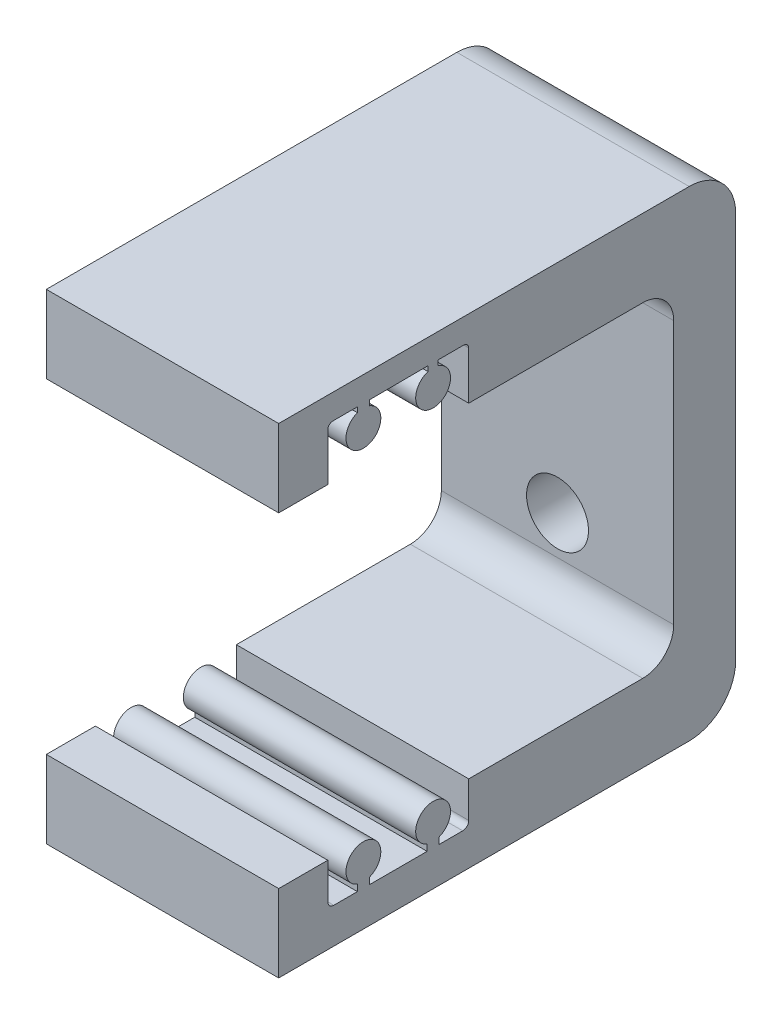
SolidWorks part; units mm, degrees
material "ABS"
ref_plane "Plano frontal" through (0, 0, 0) normal (0, 0, 1) x (1, 0, 0)
ref_plane "Plano superior" through (0, 0, 0) normal (0, 1, 0) x (1, 0, 0)
ref_plane "Plano direito" through (0, 0, 0) normal (1, 0, 0) x (0, 0, -1)
sketch "Esboço1" plane through (0, 0, 0) normal (0, 0, 1) x (1, 0, 0)
  line L0 (-15, 31) -> (-15, -31)
  line L1 (-15, -21) -> (15, -21)
  line L2 (-15, -21) -> (-15, 21)
  line L3 (-15, 21) -> (15, 21)
  line L4 (15, -21) -> (15, 21)
  line L5 (-15, -21) -> (15, 21) construction
  line L6 (-15, 21) -> (15, -21) construction
  line L7 (-15, -31) -> (15, -31)
  line L8 (15, -31) -> (15, 31)
  line L9 (15, 31) -> (-15, 31)
  point P0 (0, 0)
  point P10 (-15, 0)
  dimension "D1" = 42
  dimension "D2" = 30
  dimension "D3" = 10
extrude "Ressalto-extrusão1" add sketch "Esboço1" along normal blind 59 contours L8 L9 L0 L3 | L7 L8 L1 L0
sketch "Esboço2" plane through (0, 0, 0) normal (0, 0, -1) x (-1, 0, 0)
  line L0 (15, -21) -> (-15, -21) construction
  line L1 (15, 31) -> (15, -31) construction
  line L2 (15, 21) -> (-15, 21) construction
  line L3 (-15, -21) -> (-15, 21) construction
  line L4 (15, -21) -> (-15, -21)
  line L5 (15, 31) -> (15, -31)
  line L6 (15, 21) -> (-15, 21)
  line L7 (-15, -21) -> (-15, 21)
  line L8 (-15, 21) -> (-15, 31)
  line L9 (-15, 31) -> (15, 31)
  line L10 (-15, -21) -> (-15, -31)
  line L11 (-15, -31) -> (15, -31)
  line L12 (15, -21) -> (-15, -21)
  line L13 (-15, 21) -> (15, 21)
  line L14 (15, -21) -> (-15, -21)
  line M2 (-15, 21) -> (15, 21)
extrude "Ressalto-extrusão2" add sketch "Esboço2" against normal blind 8 contours L7 L4 L5 M2
sketch "Esboço3" plane through (-15, 0, 0) normal (-1, 0, 0) x (0, 0, 1)
  line L0 (31.2729, 21) -> (33.5, 21)
  line L1 (59, 21) -> (8, 21) construction
  line L2 (34.4643, 21) -> (34.4643, 27.1808)
  line L3 (38.4075, 27.8215) -> (38.4075, 27.1622)
  line L4 (39.7211, 27.8215) -> (39.7211, 27.1622)
  line L6 (0, 0) -> (64.8544, 0) construction
  line L7 (47.295, 27.1246) -> (47.295, 27.7839)
  line L8 (48.8337, 27.1246) -> (48.8337, 27.7839)
  line L9 (52.5643, 26.27) -> (52.5643, 20.7683) construction
  line L10 (52.5643, 21) -> (54.6977, 21)
  line L11 (33.5, 21) -> (52.5643, 21)
  line L13 (35.105, 27.8215) -> (38.1075, 27.8215)
  line L14 (38.1075, 27.8215) -> (40.0211, 27.8215)
  line L15 (40.0211, 27.8215) -> (48.8534, 27.7758)
  line L16 (48.8534, 27.7758) -> (48.8337, 27.7839)
  line L17 (48.8337, 27.7839) -> (52.0143, 27.7839)
  line L18 (52.6643, 27.1338) -> (52.6643, 21)
  line L19 (0, 31) -> (0, -31) construction
  line L20 (44.3337, -27.7122) -> (44.3337, -28.817) construction
  line L21 (52.6643, -25.6493) -> (52.6643, -20.77)
  line L22 (49.2154, -26.4238) -> (51.8898, -26.4238)
  line L23 (48.5337, -26.4238) -> (49.2154, -26.4238)
  line L24 (40.1337, -26.4238) -> (48.5337, -26.4238)
  line L25 (37.995, -26.4238) -> (40.1337, -26.4238)
  line L26 (35.2389, -26.4238) -> (37.995, -26.4238)
  line L27 (34.4643, -20.7704) -> (34.4643, -25.6493)
  line L28 (34.5, -20.77) -> (52.5643, -20.77)
  line L29 (52.5643, -20.77) -> (54.6977, -20.77)
  line L30 (47.295, -25.5846) -> (47.295, -26.4238)
  line L31 (48.8337, -27.7122) -> (48.8337, -25.5846)
  line L32 (39.8337, -26.4238) -> (39.8337, -25.5846)
  line L33 (38.295, -26.4238) -> (38.295, -25.5846)
  line L34 (34.4643, -20.7704) -> (34.5, -20.77)
  line L35 (31.2729, -20.77) -> (34.5, -20.77)
  line L36 (34.5643, 20.7683) -> (34.5643, 26.27) construction
  line L37 (34.5643, -19.2283) -> (34.5643, -24.73) construction
  line L38 (34.4643, -20.7704) -> (34.5, -20.77)
  line L39 (52.6643, -20.77) -> (52.5643, -20.77)
  line L40 (46.995, -25.73) -> (46.995, -26.4238) construction
  line L41 (49.1337, -25.73) -> (49.1337, -26.4238) construction
  line L42 (40.1337, -25.73) -> (40.1337, -26.4238) construction
  line L43 (37.995, -25.73) -> (37.995, -26.4238) construction
  arc A0 (38.4075, 27.1622) -> (39.7211, 27.1622) centre (39.0643, 25.0102) ccw
  arc A1 (47.295, 27.1246) -> (48.8337, 27.1246) centre (48.0643, 25.0102) ccw
  arc A2 (51.8898, -26.4238) -> (52.6643, -25.6493) centre (51.8898, -25.6493) ccw
  arc A3 (34.4643, -25.6493) -> (35.2389, -26.4238) centre (35.2389, -25.6493) ccw
  arc A4 (35.105, 27.8215) -> (34.4643, 27.1622) centre (35.1143, 27.1715) ccw
  arc A5 (52.0143, 27.7839) -> (52.6643, 27.1338) centre (52.0143, 27.1338) cw
  arc A7 (38.295, -25.5846) -> (39.8337, -25.5846) centre (39.0643, -23.4702) cw
  arc A8 (48.8337, -25.5846) -> (47.295, -25.5846) centre (48.0643, -23.4702) ccw
  point P11 (48.0643, -23.4702)
  point P19 (49.1337, 27.27)
  point P20 (46.995, 27.27)
  point P78 (39.0643, -23.4702)
  point P88 (37.995, -26.0769)
  line M13 (59, -21) -> (8, -21)
  line M15 (8, 21) -> (59, 21)
  dimension "D2" = 4.5
  dimension "D9" = 4.5
  dimension "D10" = 0.1
  dimension "D11" = 0.1
  dimension "D12" = 2.25
  dimension "D3" = 0.3
  dimension "D4" = 0.3
  dimension "D1" = 0.1
  dimension "D5" = 0.1
  dimension "D6" = 0.3
  dimension "D7" = 0.3
  dimension "D8" = 0.3
extrude "Corte-extrusão1" cut sketch "Esboço3" against normal through all contours A8 L31 L23 L22 A2 L21 L34 L27 A3 L26 L25 L33 A7 L32 L24 L30 M13 | A5 L17 L16 L15 L8 A1 L7 L14 L4 A0 L3 L13 A4 L2 L0 L18 M15
sketch "Esboço4" plane through (-15, 0, 0) normal (-1, 0, 0) x (0, 0, 1)
  line L0 (47.295, 27.7839) -> (48.8534, 27.7758)
  line L1 (48.8534, 27.7758) -> (48.8534, 27.1173)
  line L3 (47.2916, 27.1234) -> (47.295, 27.7839)
  line L4 (38.4075, 27.8215) -> (38.4075, 27.1622)
  line L6 (39.7211, 27.1622) -> (39.7211, 27.8215)
  line L7 (39.7211, 27.8215) -> (38.4075, 27.8215)
  arc A0 (38.4075, 27.1622) -> (39.7211, 27.1622) centre (39.0643, 25.0102) ccw
  arc A1 (47.2916, 27.1234) -> (48.8534, 27.1173) centre (48.0643, 25.0102) ccw
extrude "Corte-extrusão2" cut sketch "Esboço4" against normal blind 4
fillet "Filete1" radius 4 2 edges at (0, 21, 8) (0, -21, 8)
sketch "Esboço5" plane through (0, 0, 0) normal (0, 0, -1) x (-1, 0, 0)
  line L0 (-15, 0) -> (15, 0) construction
  line L4 (-15, 31) -> (-15, -31)
  line L5 (-15, -31) -> (15, -31)
  line L6 (15, -31) -> (15, 31)
  line L7 (15, 31) -> (-15, 31)
  line L8 (-15, 31) -> (-15, -31)
  line L9 (-15, -31) -> (15, -31)
  line L10 (15, -31) -> (15, 31)
  line L11 (15, 31) -> (-15, 31)
  circle A0 centre (0, -12) radius 4
  circle A1 centre (0, 12) radius 4
  dimension "D2" = 8
  dimension "D3" = 15
  dimension "D4" = 12
  dimension "D1" = 0
extrude "Corte-extrusão3" cut sketch "Esboço5" against normal through all contours A1 | A0
fillet "Filete2" radius 6 2 edges at (0, -31, 0) (0, 31, 0)
